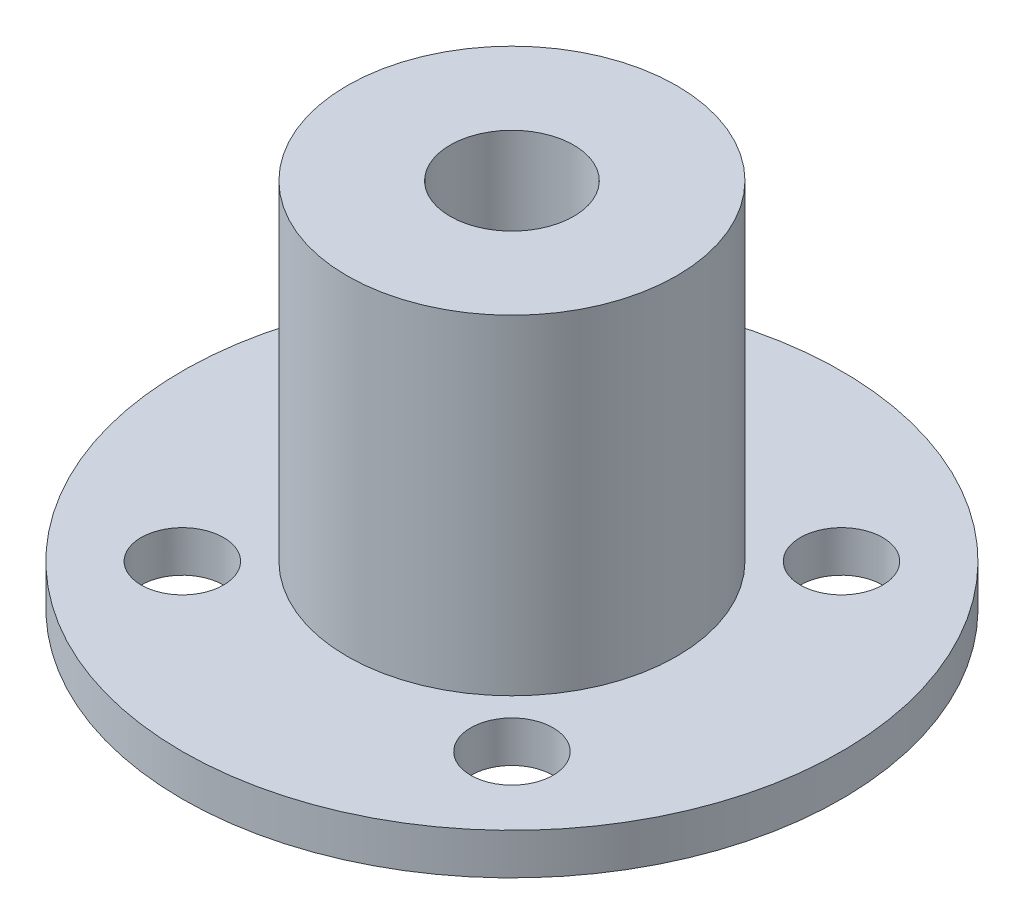
SolidWorks part; units mm, degrees
material "1060 Alloy"
ref_plane "Front Plane" through (0, 0, 0) normal (0, 0, 1) x (1, 0, 0)
ref_plane "Top Plane" through (0, 0, 0) normal (0, 1, 0) x (1, 0, 0)
ref_plane "Right Plane" through (0, 0, 0) normal (1, 0, 0) x (0, 0, -1)
sketch "Sketch1" plane through (0, 0, 0) normal (0, 1, 0) x (1, 0, 0)
  circle A0 centre (0, 0) radius 25.4
  dimension "D1" = 50.8
extrude "Boss-Extrude1" add sketch "Sketch1" along normal blind 3.175
sketch "Sketch2" plane through (0, 3.175, 0) normal (0, 1, 0) x (1, 0, 0)
  line L0 (0, 0) -> (0, 12.7) construction
  circle A0 centre (0, 0) radius 4.7625
  circle A1 centre (0, 0) radius 12.7
  dimension "D1" = 9.525
  dimension "D2" = 25.4
extrude "Boss-Extrude2" add sketch "Sketch2" along normal blind 25.4
sketch "Sketch3" plane through (0, 0, 0) normal (0, -1, 0) x (1, 0, 0)
  line L0 (-25.4, 0) -> (25.4, 0) construction
  line L1 (-12.7, 0) -> (-12.7, 12.7) construction
  line L2 (0, 0) -> (0, 25.4) construction
  circle A1 centre (0, 0) radius 25.4 construction
  circle A2 centre (-12.7, 12.7) radius 3.175
  circle A3 centre (12.7, 12.7) radius 3.175
  circle A4 centre (12.7, -12.7) radius 3.175
  circle A5 centre (-12.7, -12.7) radius 3.175
  dimension "D1" = 6.35
  dimension "D2" = 12.7
  dimension "D3" = 12.7
extrude "Cut-Extrude1" cut sketch "Sketch3" against normal through all
